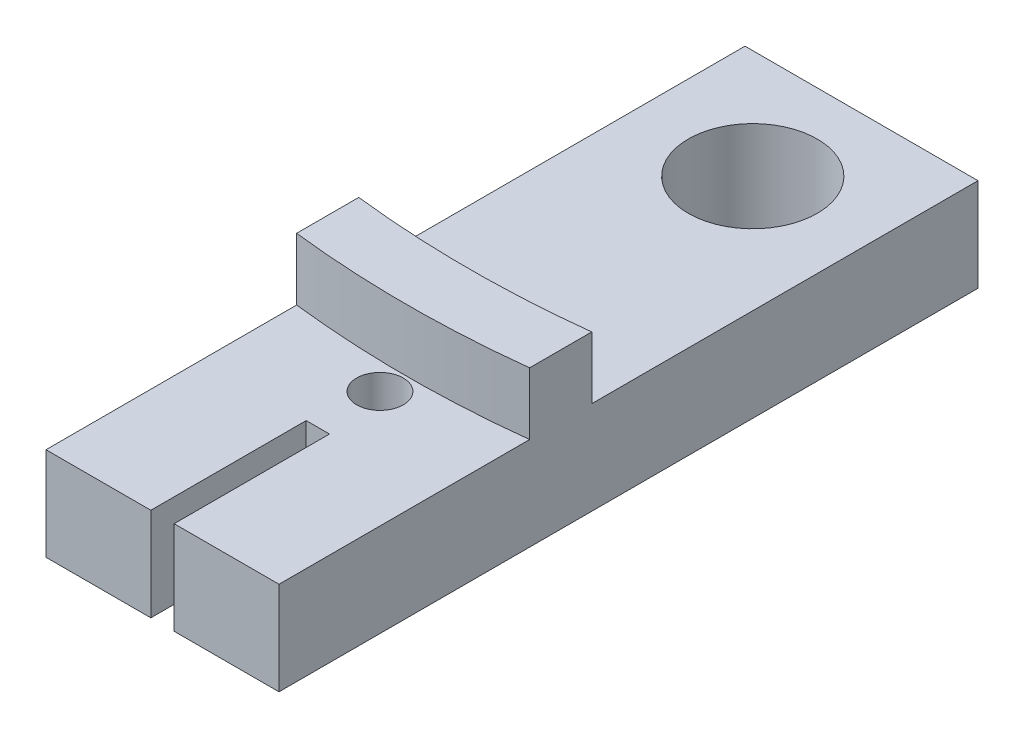
SolidWorks part; units mm, degrees
ref_plane "Спереди" through (0, 0, 0) normal (0, 0, 1) x (1, 0, 0)
ref_plane "Сверху" through (0, 0, 0) normal (0, 1, 0) x (1, 0, 0)
ref_plane "Справа" through (0, 0, 0) normal (1, 0, 0) x (0, 0, -1)
sketch "Sketch1" plane through (0, 0, 0) normal (0, 1, 0) x (1, 0, 0)
  line L0 (0, 17.5) -> (0, -17.5) construction
  line L1 (7.5, -17.5) -> (-7.5, -17.5)
  line L2 (7.5, -17.5) -> (7.5, 17.5)
  line L3 (7.5, 17.5) -> (-7.5, 17.5)
  line L4 (-7.5, -17.5) -> (-7.5, 17.5)
  line L5 (7.5, -17.5) -> (-7.5, 17.5) construction
  line L6 (7.5, 17.5) -> (-7.5, -17.5) construction
  circle A0 centre (0, 10.5) radius 4.15
  circle A1 centre (0, -13.5) radius 1.5
  point P0 (0, 0)
  dimension "D1" = 8.3
  dimension "D5" = 3
  dimension "D2" = 7
  dimension "D3" = 35
  dimension "D4" = 15
  dimension "D6" = 4
extrude "Boss-Extrude1" add sketch "Sketch1" along normal blind 6
sketch "Sketch2" plane through (0, 6, 0) normal (0, 1, 0) x (1, 0, 0)
  line L0 (0, -17.5) -> (0, 17.5) construction
  line L1 (-7.5, -17.5) -> (7.5, -17.5) construction
  line L2 (7.5, 17.5) -> (-7.5, 17.5) construction
  line L3 (7.5, -17.5) -> (7.5, 17.5) construction
  line L4 (-7.5, 17.5) -> (-7.5, -17.5) construction
  line L5 (-7.5, -11.3659) -> (-7.5, -7.3659)
  line L6 (7.5, -7.3659) -> (7.5, -11.3659)
  arc A0 (7.5, -7.3659) -> (-7.5, -7.3659) centre (0, 57.2) cw
  arc A1 (-7.5, -11.3659) -> (7.5, -11.3659) centre (0, 53.2) ccw
  point P16 (0, -7.8)
  dimension "D2" = 65
  dimension "D3" = 9.7
  dimension "D1" = 4
extrude "Boss-Extrude2" add sketch "Sketch2" along normal blind 4
sketch "Sketch3" plane through (0, 0, 17.5) normal (0, 0, 1) x (1, 0, 0)
  line L0 (7.5, 3) -> (-7.5, 3) construction
  line L1 (7.5, 6) -> (7.5, 0) construction
  line L2 (-7.5, 6) -> (-7.5, 0) construction
  line L4 (0.75, 6) -> (7.5, 6)
  line L5 (0.75, 6) -> (0.75, 0)
  line L6 (0.75, 0) -> (7.5, 0)
  line L7 (7.5, 6) -> (7.5, 0)
  line L8 (0.75, 6) -> (7.5, 0) construction
  line L9 (0.75, 0) -> (7.5, 6) construction
  line L10 (-0.75, 6) -> (-7.5, 6)
  line L11 (-0.75, 6) -> (-0.75, 0)
  line L12 (-0.75, 0) -> (-7.5, 0)
  line L13 (-7.5, 6) -> (-7.5, 0)
  line L14 (-0.75, 6) -> (-7.5, 0) construction
  line L15 (-0.75, 0) -> (-7.5, 6) construction
  point P6 (4.125, 3)
  point P12 (-4.125, 3)
  dimension "D1" = 1.5
extrude "Boss-Extrude3" add sketch "Sketch3" along normal blind 10
